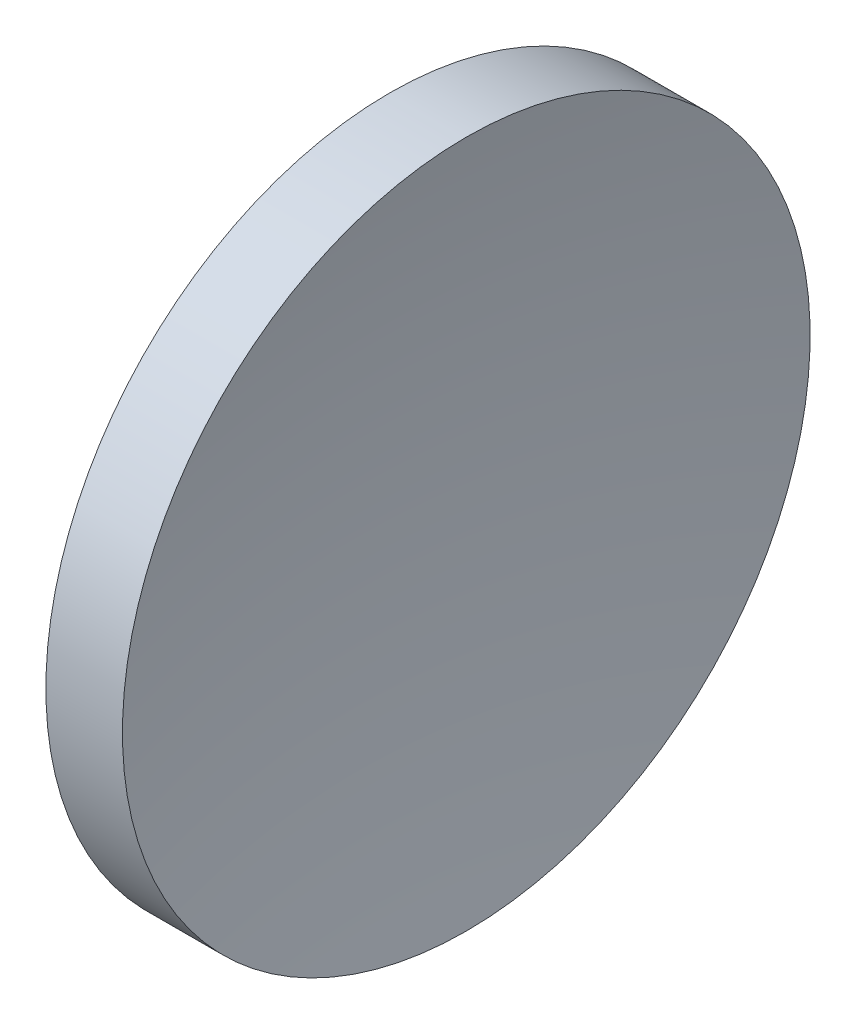
SolidWorks part; units mm, degrees
ref_plane "前视基准面" through (0, 0, 0) normal (0, 0, 1) x (1, 0, 0)
ref_plane "上视基准面" through (0, 0, 0) normal (0, 1, 0) x (1, 0, 0)
ref_plane "右视基准面" through (0, 0, 0) normal (1, 0, 0) x (0, 0, -1)
sketch "草图1" plane through (0, 0, 0) normal (0, 0, 1) x (1, 0, 0)
  line L0 (110.0148, 65.1575) -> (131.4016, 65.1575) construction
  line L1 (114.9754, 65.1575) -> (114.9754, 85.1575)
  line L2 (114.9754, 85.1575) -> (119.4304, 85.1575)
  line L3 (117.4754, 65.1575) -> (114.9754, 65.1575)
  arc A0 (119.4304, 85.1575) -> (117.4754, 65.1575) centre (220.7554, 65.1575) ccw
revolve "旋转1" add sketch "草图1" angle 360 about L0
